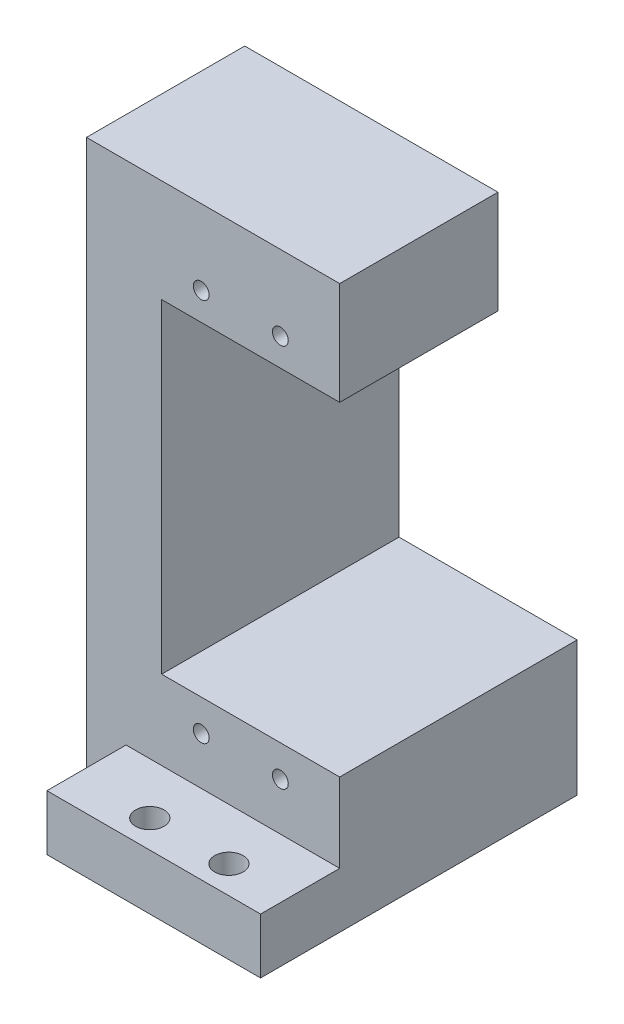
SolidWorks part; units mm, degrees
ref_plane "Front Plane" through (0, 0, 0) normal (0, 0, 1) x (1, 0, 0)
ref_plane "Top Plane" through (0, 0, 0) normal (0, 1, 0) x (1, 0, 0)
ref_plane "Right Plane" through (0, 0, 0) normal (1, 0, 0) x (0, 0, -1)
sketch "Sketch1" plane through (0, 0, 0) normal (0, 1, 0) x (1, 0, 0)
  line L1 (0, 0) -> (25, 0)
  line L2 (0, 0) -> (0, 40)
  line L3 (0, 40) -> (25, 40)
  line L4 (25, 0) -> (25, 40)
  dimension "D1" = 25
  dimension "D2" = 40
extrude "Boss-Extrude1" add sketch "Sketch1" along normal blind 50
sketch "Sketch2" plane through (0, 50, 0) normal (0, 1, 0) x (1, 0, 0)
  line L0 (0, 0) -> (25, 0) construction
  line L1 (2.5, 0) -> (25, 0)
  line L2 (2.5, 0) -> (2.5, 40)
  line L3 (2.5, 40) -> (25, 40)
  line L4 (25, 0) -> (25, 40)
  line L5 (25, 40) -> (0, 40) construction
  dimension "D1" = 22.5
  dimension "D2" = 2.5
  dimension "D3" = 0
extrude "Cut-Extrude1" cut sketch "Sketch2" against normal blind 25
sketch "Sketch3" plane through (0, 0, 0) normal (0, 0, 1) x (1, 0, 0)
  line L1 (2.5, 25) -> (22.5, 25)
  line L2 (2.5, 25) -> (2.5, 15)
  line L3 (2.5, 15) -> (22.5, 15)
  line L4 (22.5, 25) -> (22.5, 15)
  dimension "D1" = 10
  dimension "D2" = 20
extrude "Cut-Extrude2" cut sketch "Sketch3" against normal blind 10
sketch "Sketch5" plane through (0, 0, -10) normal (0, 0, 1) x (1, 0, 0)
  line L0 (2.5, 15) -> (2.5, 50) construction
  line L3 (22.5, 25) -> (2.5, 25) construction
  line L4 (22.5, 15) -> (22.5, 25) construction
  circle A0 centre (7.5, 21) radius 1
  circle A1 centre (17.5, 21) radius 1
  dimension "D2" = 2
  dimension "D4" = 2
  dimension "D1" = 5
  dimension "D3" = 4
  dimension "D5" = 4
  dimension "D6" = 5
extrude "Cut-Extrude4" cut sketch "Sketch5" against normal blind 12
sketch "Sketch6" plane through (0, 0, 0) normal (0, -1, 0) x (1, 0, 0)
  line L1 (0, 0) -> (25, 0)
  line L2 (0, 0) -> (0, -40)
  line L3 (0, -40) -> (25, -40)
  line L4 (25, 0) -> (25, -40)
extrude "Cut-Extrude5" cut sketch "Sketch6" against normal blind 8
sketch "Sketch7" plane through (0, 8, 0) normal (0, -1, 0) x (1, 0, 0)
  line L0 (25, 0) -> (0, 0) construction
  line L1 (2.5, -37.5) -> (22.5, -37.5)
  line L2 (2.5, -37.5) -> (2.5, -15)
  line L3 (2.5, -15) -> (22.5, -15)
  line L4 (22.5, -37.5) -> (22.5, -15)
  line L5 (0, 0) -> (0, -40) construction
  line L6 (25, -40) -> (25, 0) construction
  dimension "D1" = 15
  dimension "D2" = 22.5
  dimension "D3" = 2.5
  dimension "D4" = 2.5
extrude "Cut-Extrude6" cut sketch "Sketch7" against normal blind 8
sketch "Sketch8" plane through (0, 15, 0) normal (0, 1, 0) x (1, 0, 0)
  line L0 (2.5, 10) -> (22.5, 10) construction
  line L2 (2.5, 10) -> (2.5, 0) construction
  line L3 (22.5, 10) -> (22.5, 0) construction
  circle A0 centre (7.5, 3.5) radius 1.8
  circle A1 centre (17.5, 3.5) radius 1.8
  dimension "D1" = 3.6
  dimension "D2" = 3.6
  dimension "D3" = 6.5
  dimension "D4" = 6.5
  dimension "D5" = 5
  dimension "D6" = 5
extrude "Cut-Extrude7" cut sketch "Sketch8" against normal through all
sketch "Sketch12" plane through (22.5, 0, 0) normal (-1, 0, 0) x (0, 0, 1)
  line L1 (-10, 15) -> (0, 15)
  line L2 (-10, 15) -> (-10, 25)
  line L3 (-10, 25) -> (0, 25)
  line L4 (0, 15) -> (0, 25)
extrude "Cut-Extrude9" cut sketch "Sketch12" against normal blind 10
sketch "Sketch13" plane through (0, 50, 0) normal (0, 1, 0) x (1, 0, 0)
  line L1 (0, 40) -> (2.5, 40)
  line L2 (0, 40) -> (0, 0)
  line L3 (0, 0) -> (2.5, 0)
  line L4 (2.5, 40) -> (2.5, 0)
extrude "Boss-Extrude2" add sketch "Sketch13" along normal blind 19
sketch "Sketch14" plane through (0, 0, 0) normal (-1, 0, 0) x (0, 0, 1)
  line L0 (-40, 69) -> (0, 69) construction
  line L1 (-40, 69) -> (0, 69)
  line L2 (-40, 69) -> (-40, 8)
  line L3 (-40, 8) -> (0, 8)
  line L4 (0, 69) -> (0, 8)
  line L5 (-40, 69) -> (-40, 8) construction
extrude "Boss-Extrude3" add sketch "Sketch14" along normal blind 2
sketch "Sketch15" plane through (2.5, 0, 0) normal (1, 0, 0) x (0, 0, -1)
  line L0 (40, 25) -> (40, 69) construction
  line L1 (0, 69) -> (40, 69)
  line L2 (0, 69) -> (0, 66)
  line L3 (0, 66) -> (40, 66)
  line L4 (40, 69) -> (40, 66)
  dimension "D1" = 3
extrude "Boss-Extrude4" add sketch "Sketch15" along normal up to surface (22.5 mm away) up to face at (25, 16, -16.6667)
sketch "Sketch16" plane through (25, 0, 0) normal (1, 0, 0) x (0, 0, -1)
  line L0 (0, 66) -> (40, 66) construction
  line L1 (0, 69) -> (10, 69)
  line L2 (0, 69) -> (0, 66)
  line L3 (0, 66) -> (10, 66)
  line L4 (10, 69) -> (10, 66)
extrude "Cut-Extrude10" cut sketch "Sketch16" against normal up to surface (22.5 mm away) up to face at (2.5, 35.3333, -16.6667)
sketch "Sketch17" plane through (2.5, 0, 0) normal (1, 0, 0) x (0, 0, -1)
  line L1 (0, 69) -> (10, 69)
  line L2 (0, 69) -> (0, 15)
  line L3 (0, 15) -> (10, 15)
  line L4 (10, 69) -> (10, 15)
extrude "Cut-Extrude11" cut sketch "Sketch17" against normal through all
sketch "Sketch18" plane through (0, 69, 0) normal (0, 1, 0) x (1, 0, 0)
  line L1 (-2, 10) -> (25, 10)
  line L2 (-2, 10) -> (-2, 40)
  line L3 (-2, 40) -> (25, 40)
  line L4 (25, 10) -> (25, 40)
extrude "Boss-Extrude5" add sketch "Sketch18" along normal blind 10
ref_plane "Plane1" through (0, 45.25, 0) normal (0, -1, 0) x (-1, 0, 0)
mirror "Mirror1" about plane through (0, 45.25, 0) normal (0, -1, 0) of "Cut-Extrude4"
sketch "Sketch19" plane through (-2, 0, 0) normal (-1, 0, 0) x (0, 0, 1)
  line L0 (-40, 8) -> (0, 8) construction
  line L1 (-40, 79) -> (-10, 79)
  line L2 (-40, 79) -> (-40, 8)
  line L3 (-40, 8) -> (-10, 8)
  line L4 (-10, 79) -> (-10, 8)
  dimension "D1" = 30
extrude "Boss-Extrude6" add sketch "Sketch19" along normal blind 5
sketch "Sketch20" plane through (0, 79, 0) normal (0, 1, 0) x (1, 0, 0)
  line L0 (25, 10) -> (25, 40) construction
  line L1 (-7, 40) -> (25, 40)
  line L2 (-7, 40) -> (-7, 30)
  line L3 (-7, 30) -> (25, 30)
  line L4 (25, 40) -> (25, 30)
  line L5 (-2, 10) -> (25, 10) construction
  dimension "D1" = 20
extrude "Cut-Extrude12" cut sketch "Sketch20" against normal up to surface (13 mm away) up to face at (13.75, 66, -25)
